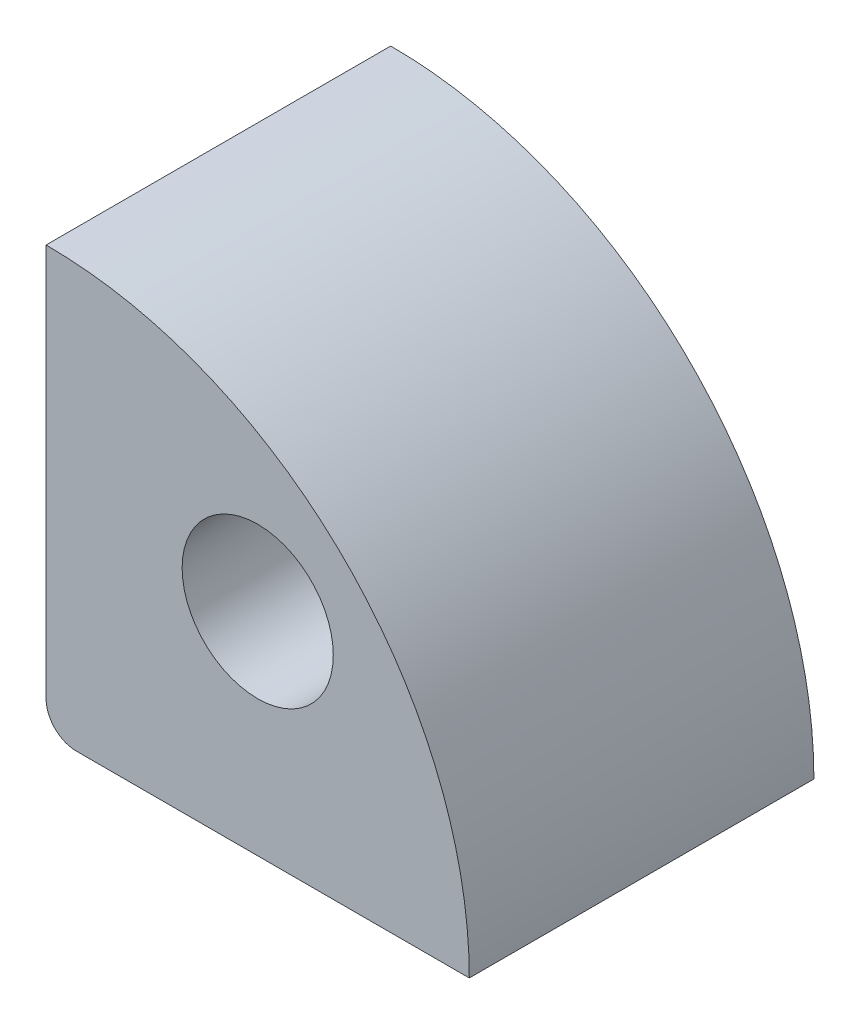
SolidWorks part; units mm, degrees
ref_plane "Přední rovina" through (0, 0, 0) normal (0, 0, 1) x (1, 0, 0)
ref_plane "Horní rovina" through (0, 0, 0) normal (0, 1, 0) x (1, 0, 0)
ref_plane "Pravá rovina" through (0, 0, 0) normal (1, 0, 0) x (0, 0, -1)
sketch "Skica1" plane through (0, 0, 0) normal (0, 0, 1) x (1, 0, 0)
  line L0 (0, 0) -> (7, 0)
  line L1 (0, 0) -> (0, 7)
  arc A0 (7, 0) -> (0, 7) centre (0, 0) ccw
  dimension "D1" = 7
extrude "Přidat vysunutím1" add sketch "Skica1" along normal blind 5.7
sketch "Skica2" plane through (0, 0, 5.7) normal (0, 0, 1) x (1, 0, 0)
  line L0 (0, 0) -> (3.5002, 3.5002) construction
  line L1 (0, 0) -> (7, 0) construction
  circle A0 centre (3.5002, 3.5002) radius 1.25
  dimension "D3" = 2.5
  dimension "D1" = 4.95
  dimension "D2" = 45
extrude "Odebrat vysunutím1" cut sketch "Skica2" against normal through all
fillet "Zaoblit1" radius 0.5 1 edges at (0, 0, 2.85)
